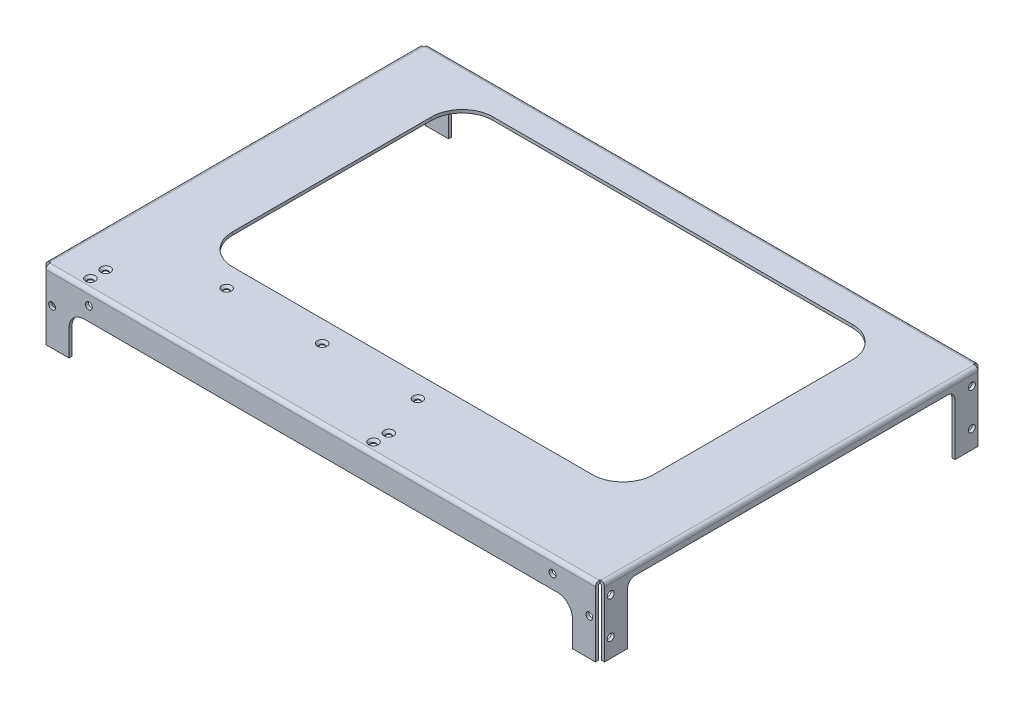
SolidWorks part; units mm, degrees
material "6061-T6 (SS)"
ref_plane "Front Plane" through (0, 0, 0) normal (0, 0, 1) x (1, 0, 0)
ref_plane "Top Plane" through (0, 0, 0) normal (0, 1, 0) x (1, 0, 0)
ref_plane "Right Plane" through (0, 0, 0) normal (1, 0, 0) x (0, 0, -1)
sketch "Sketch1" plane through (0, 0, 0) normal (1, 0, 0) x (0, 0, -1)
  line L0 (123, -45) -> (125, -45)
  line L1 (-122.5, 0) -> (122.5, 0)
  line L2 (-125, -2.5) -> (-125, -45)
  line L3 (-125, -45) -> (-123, -45)
  line L4 (125, -2.5) -> (125, -45)
  line L6 (-123, -45) -> (-123, -2.5)
  line L7 (-122.5, -2) -> (122.5, -2)
  line L8 (123, -45) -> (123, -2.5)
  arc A0 (-122.5, 0) -> (-125, -2.5) centre (-122.5, -2.5) ccw
  arc A1 (122.5, 0) -> (125, -2.5) centre (122.5, -2.5) cw
  arc A2 (122.5, -2) -> (123, -2.5) centre (122.5, -2.5) cw
  arc A3 (-123, -2.5) -> (-122.5, -2) centre (-122.5, -2.5) cw
  dimension "D1" = 2.5
  dimension "D2" = 250
  dimension "D3" = 2
  dimension "D4" = 45
extrude "Boss-Extrude1" add sketch "Sketch1" along normal mid plane 365
sketch "Sketch2" plane through (0, 0, 125) normal (0, 0, 1) x (1, 0, 0)
  line L0 (182.5, -45) -> (-182.5, -45) construction
  line L1 (-164.5, -45) -> (164.5, -45)
  line L2 (-164.5, -45) -> (-164.5, -28)
  line L3 (-154.5, -18) -> (154.5, -18)
  line L4 (164.5, -45) -> (164.5, -28)
  line L5 (182.5, 0) -> (-182.5, 0) construction
  line L6 (-182.5, -2.5) -> (-182.5, -45) construction
  line L7 (182.5, -2.5) -> (182.5, -45) construction
  arc A0 (154.5, -18) -> (164.5, -28) centre (154.5, -28) cw
  arc A1 (-164.5, -28) -> (-154.5, -18) centre (-154.5, -28) cw
  dimension "D4" = 10
  dimension "D1" = 18
  dimension "D2" = 18
  dimension "D3" = 18
extrude "Cut-Extrude1" cut sketch "Sketch2" against normal through all
sketch "Sketch3" plane through (0, 0, 0) normal (0, 1, 0) x (1, 0, 0)
  line L0 (-182.5, 122.5) -> (-182.5, -122.5) construction
  line L1 (-117.5, 105) -> (117.5, 105)
  line L2 (-137.5, 85) -> (-137.5, -45)
  line L3 (-117.5, -65) -> (117.5, -65)
  line L4 (137.5, 85) -> (137.5, -45)
  line L5 (182.5, 122.5) -> (182.5, -122.5) construction
  line L6 (182.5, 125) -> (-182.5, 125) construction
  line L7 (182.5, -125) -> (-182.5, -125) construction
  arc A0 (117.5, 105) -> (137.5, 85) centre (117.5, 85) cw
  arc A1 (137.5, -45) -> (117.5, -65) centre (117.5, -45) cw
  arc A2 (-137.5, -45) -> (-117.5, -65) centre (-117.5, -45) ccw
  arc A3 (-117.5, 105) -> (-137.5, 85) centre (-117.5, 85) ccw
  dimension "D1" = 20
  dimension "D2" = 45
  dimension "D3" = 45
  dimension "D4" = 20
  dimension "D5" = 60
extrude "Cut-Extrude2" cut sketch "Sketch3" against normal blind 10
sketch "Sketch4" plane through (0, -2, 0) normal (0, -1, 0) x (1, 0, 0)
  line L0 (182.5, -123) -> (-182.5, -123) construction
  line L1 (-182.5, 123) -> (-180.5, 123)
  line L2 (-182.5, 123) -> (-182.5, -123)
  line L3 (-182.5, -123) -> (-180.5, -123)
  line L4 (-180.5, 123) -> (-180.5, -123)
  line L5 (182.5, 123) -> (164.5, 123) construction
  line L6 (182.5, -123) -> (180.5, -123)
  line L7 (182.5, -123) -> (182.5, 123)
  line L8 (182.5, 123) -> (180.5, 123)
  line L9 (180.5, -123) -> (180.5, 123)
  dimension "D1" = 2
extrude "Boss-Extrude2" add sketch "Sketch4" along normal up to surface (43 mm away) up to face at (-173.5, -45, 124)
sketch "Sketch5" plane through (0, -45, 0) normal (0, -1, 0) x (1, 0, 0)
  line L1 (-182.5, 125) -> (-179.5, 125)
  line L2 (-182.5, 125) -> (-182.5, 122)
  line L3 (-182.5, 122) -> (-179.5, 122)
  line L4 (-179.5, 125) -> (-179.5, 122)
  line L5 (-182.5, -125) -> (-179.5, -125)
  line L6 (-182.5, -125) -> (-182.5, -122)
  line L7 (-182.5, -122) -> (-179.5, -122)
  line L8 (-179.5, -125) -> (-179.5, -122)
  line L9 (182.5, -125) -> (179.5, -125)
  line L10 (182.5, -125) -> (182.5, -122)
  line L11 (182.5, -122) -> (179.5, -122)
  line L12 (179.5, -125) -> (179.5, -122)
  line L13 (182.5, 125) -> (179.5, 125)
  line L14 (182.5, 125) -> (182.5, 122)
  line L15 (182.5, 122) -> (179.5, 122)
  line L16 (179.5, 125) -> (179.5, 122)
  dimension "D1" = 3
extrude "Cut-Extrude3" cut sketch "Sketch5" against normal through all
fillet "Fillet1" radius 0.5 2 edges at (180.5, -2, 0) (-180.5, -2, 0)
fillet "Fillet2" radius 2.5 2 edges at (182.5, 0, 0) (-182.5, 0, 0)
sketch "Sketch8" plane through (-182.5, 0, 0) normal (-1, 0, 0) x (0, 0, 1)
  line L0 (122, -45) -> (-122, -45) construction
  line L1 (-107, -45) -> (107, -45)
  line L2 (-107, -45) -> (-107, -11)
  line L3 (-102, -6) -> (102, -6)
  line L4 (107, -45) -> (107, -11)
  line L5 (-125, -2.5) -> (-125, -45) construction
  line L6 (125, -45) -> (125, -28) construction
  line L7 (-122, 0) -> (122, 0) construction
  arc A0 (102, -6) -> (107, -11) centre (102, -11) cw
  arc A1 (-107, -11) -> (-102, -6) centre (-102, -11) cw
  dimension "D4" = 5
  dimension "D1" = 18
  dimension "D2" = 18
  dimension "D3" = 6
extrude "Cut-Extrude6" cut sketch "Sketch8" against normal through all
sketch "Sketch9" plane through (-182.5, 0, 0) normal (-1, 0, 0) x (0, 0, 1)
  circle A0 centre (-118, -9) radius 2.25
  circle A1 centre (-118, -33) radius 2.25
  circle A2 centre (118, -9) radius 2.25
  circle A3 centre (118, -33) radius 2.25
  dimension "D1" = 4.5
extrude "Cut-Extrude7" cut sketch "Sketch9" against normal through all
sketch "Sketch10" plane through (0, 0, 125) normal (0, 0, 1) x (1, 0, 0)
  circle A1 centre (-151.5, -9) radius 2.25
  circle A3 centre (175.5, -21) radius 2.25
  circle A4 centre (151.5, -9) radius 2.25
  circle A5 centre (-175.5, -21) radius 2.25
  dimension "D1" = 4.5
extrude "Cut-Extrude8" cut sketch "Sketch10" against normal blind 10
sketch "Sketch11" plane through (0, 0, -125) normal (0, 0, -1) x (-1, 0, 0)
  circle A0 centre (-175.5, -21) radius 2.25
  circle A2 centre (-151.5, -9) radius 2.25
  circle A3 centre (151.5, -9) radius 2.25
  circle A5 centre (175.5, -21) radius 2.25
  dimension "D1" = 4.5
extrude "Cut-Extrude9" cut sketch "Sketch11" against normal blind 10
sketch "Sketch12" plane through (0, 0, 0) normal (0, 1, 0) x (1, 0, 0)
  line L0 (-107.5, -65) -> (-107.5, -93) construction
  line L1 (17.5, -65) -> (17.5, -93) construction
  line L2 (179.5, -125) -> (-179.5, -125) construction
  line L3 (-182.5, -122) -> (-182.5, 122) construction
  circle A0 centre (-45, -79) radius 1.5
  circle A1 centre (17.5, -79) radius 1.5
  circle A2 centre (-107.5, -79) radius 1.5
  circle A3 centre (-157.5, -108) radius 1.5
  circle A4 centre (-157.5, -118) radius 1.5
  circle A5 centre (27.5, -108) radius 1.5
  circle A6 centre (27.5, -118) radius 1.5
  dimension "D1" = 3
  dimension "D2" = 7
  dimension "D3" = 10
  dimension "D4" = 25
  dimension "D5" = 185
extrude "Cut-Extrude10" cut sketch "Sketch12" against normal blind 10
hole_wizard "CSK for M3 Flat Head Machine Screw1" positions "Sketch14" profile "Sketch13" countersink size "M3" standard "Ansi Metric" end condition through all
sketch "Sketch14" plane through (0, 0, 0) normal (0, 1, 0) x (-1, 0, 0)
  point P0 (107.5, 79)
  point P1 (45, 79)
  point P4 (-17.5, 79)
  point P10 (157.5, 108)
  point P13 (157.5, 118)
  point P16 (-27.5, 108)
  point P19 (-27.5, 118)
sketch "Sketch13" plane through (-107.5, 0, 79) normal (1, 0, 0) x (0, 0, 1)
  line L0 (0, 0) -> (0, 45)
  line L1 (0, 45) -> (1.7, 45)
  line L2 (1.7, 45) -> (1.7, 1.45)
  line L3 (1.7, 1.45) -> (3.15, 0)
  line L5 (3.15, 0) -> (0, 0)
  line L6 (-1.7, 1.45) -> (-3.15, 0) construction
  line L11 (0, -6.35) -> (0, 107.95) construction
  dimension "Thru Hole Dia." = 3.4
  dimension "Thru Hole Depth" = 45
  dimension "Near C'Sink Dia." = 6.3
  dimension "Near C'Sink Angle" = 90
